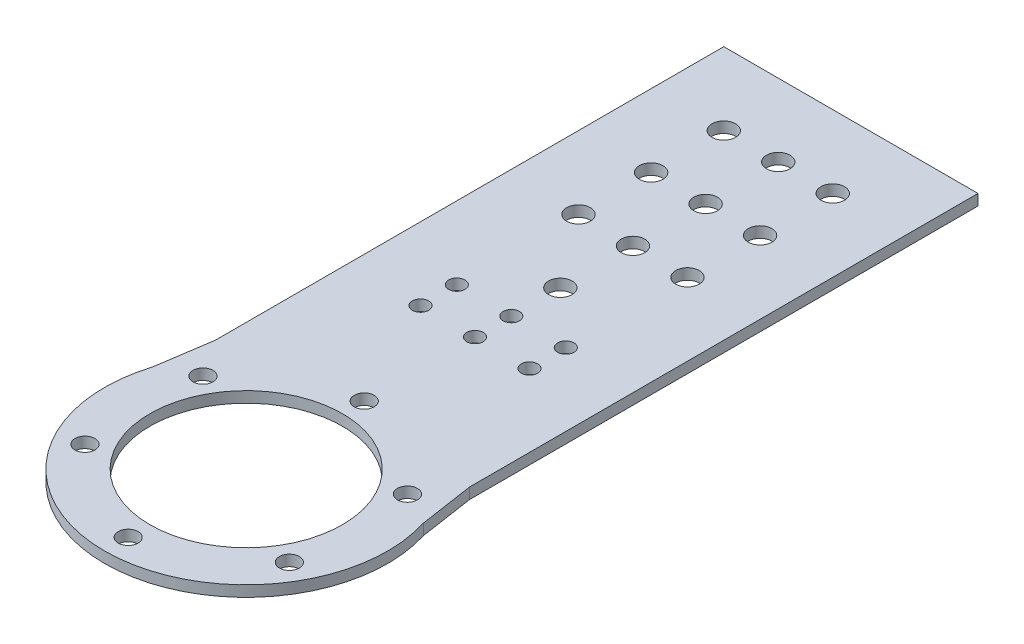
SolidWorks part; units mm, degrees
ref_plane "Front Plane" through (0, 0, 0) normal (0, 0, 1) x (1, 0, 0)
ref_plane "Top Plane" through (0, 0, 0) normal (0, 1, 0) x (1, 0, 0)
ref_plane "Right Plane" through (0, 0, 0) normal (1, 0, 0) x (0, 0, -1)
sketch "Sketch1" plane through (0, 0, 0) normal (0, 1, 0) x (1, 0, 0)
  circle A0 centre (0, 0) radius 45 construction
  circle A1 centre (0, 0) radius 39
  circle A2 centre (0, 0) radius 26.5
  circle A3 centre (0, 0) radius 32.5 construction
  dimension "D1" = 90
  dimension "D2" = 65
  dimension "D3" = 78
  dimension "D4" = 53
extrude "Boss-Extrude1" add sketch "Sketch1" along normal mid plane 3
sketch "Sketch3" plane through (0, 0, 0) normal (0, 1, 0) x (1, 0, 0)
  line L0 (0, 0) -> (0, 78) construction
  line L2 (-25, 78) -> (25, 78)
  line L3 (-25, 78) -> (-25, 26.5)
  line L4 (-25, 26.5) -> (25, 26.5)
  line L5 (25, 78) -> (25, 26.5)
  line L6 (0, 26.5) -> (0, 78) construction
  line L7 (-25, 52.25) -> (25, 52.25) construction
  circle A0 centre (0, 0) radius 26.5 construction
  point P3 (0, 52.25)
  dimension "D1" = 78
  dimension "D2" = 50
extrude "Boss-Extrude2" add sketch "Sketch3" along normal mid plane 3
sketch "Sketch4" plane through (0, 0, 0) normal (0, 1, 0) x (1, 0, 0)
  line L0 (-25, 53.9666) -> (-37.4668, 10.8276)
  line L1 (-25, 78) -> (-25, 29.9333) construction
  line L2 (-37.4668, 10.8276) -> (-25, 29.9333)
  line L3 (-25, 29.9333) -> (-25, 53.9666)
  line L4 (0, 0) -> (0, 78) construction
  line L5 (25, 78) -> (-25, 78) construction
  line L6 (37.4668, 10.8276) -> (25, 29.9333)
  line L7 (25, 53.9666) -> (37.4668, 10.8276)
  line L8 (25, 29.9333) -> (25, 53.9666)
  circle A0 centre (0, 0) radius 39 construction
extrude "Boss-Extrude3" [suppressed] add sketch "Sketch4" along normal mid plane 3
sketch "Sketch6" plane through (0, 0, 0) normal (0, 1, 0) x (1, 0, 0)
  line L0 (0, 0) -> (0, 96.5) construction
  line L1 (-35, 166.5) -> (-35, 26.5)
  line L2 (-35, 166.5) -> (35, 166.5)
  line L4 (35, 166.5) -> (35, 26.5)
  line L5 (0, 26.5) -> (0, 166.5) construction
  line L6 (-35, 96.5) -> (35, 96.5) construction
  line L7 (-35, 26.5) -> (-39, 0)
  line L8 (35, 26.5) -> (39, 0)
  line L9 (39, 0) -> (16.5208, 26.5)
  line L10 (16.5208, 26.5) -> (-14.9815, 26.5)
  line L11 (-14.9815, 26.5) -> (-39, 0)
  circle A0 centre (0, 0) radius 26.5 construction
  circle A1 centre (0, 0) radius 39 construction
  dimension "D1" = 70
  dimension "D2" = 140
extrude "Boss-Extrude4" add sketch "Sketch6" along normal mid plane 3
sketch "Sketch2" plane through (0, 0, 0) normal (0, 1, 0) x (1, 0, 0)
  circle A0 centre (0, 0) radius 32.5 construction
  circle A1 centre (0, 32.5) radius 2.75
  dimension "D1" = 65
  dimension "D2" = 5.5
extrude "Cut-Extrude1" cut sketch "Sketch2" against normal through all both and the other way through all contours A1
pattern_circular "CirPattern1" count 6 over 360 about axis through (0, 0, 0) along (0, 1, 0) of "Cut-Extrude1"
sketch "Sketch5" plane through (0, 1.5, 0) normal (0, 1, 0) x (1, 0, 0)
  line L0 (-25, 73) -> (25, 73) construction
  line L4 (35, 166.5) -> (-35, 166.5) construction
  circle A0 centre (0, 73) radius 2.25
  dimension "D1" = 4.5
  dimension "D3" = 93.5
extrude "Cut-Extrude2" cut sketch "Sketch5" against normal through all both and the other way through all
pattern_linear "LPattern1" count 2 spacing 15 along (1, 0, 0) count 2 spacing 10 along (0, 0, 1) of "Cut-Extrude2"
pattern_linear "LPattern2" count 2 spacing 15 along (-1, 0, 0) count 2 spacing 10 along (0, 0, 1) of "Cut-Extrude2"
sketch "Sketch7" plane through (0, 1.5, 0) normal (0, 1, 0) x (1, 0, 0)
  line L0 (0, 0) -> (0, 166.5) construction
  line L1 (35, 166.5) -> (-35, 166.5) construction
  line L2 (-15, 146.5) -> (15, 146.5) construction
  circle A0 centre (-15, 146.5) radius 3.25
  circle A1 centre (15, 146.5) radius 3.25
  point P8 (0, 146.5)
  dimension "D1" = 6.5
  dimension "D2" = 20
  dimension "D3" = 30
extrude "Cut-Extrude3" cut sketch "Sketch7" against normal through all both and the other way through all
pattern_linear "LPattern3" count 3 spacing 20 along (0, 0, 1) of "Cut-Extrude3"
sketch "Sketch8" plane through (0, 1.5, 0) normal (0, 1, 0) x (1, 0, 0)
  line L0 (0, 0) -> (0, 166.5) construction
  line L1 (35, 166.5) -> (-35, 166.5) construction
  circle A0 centre (0, 146.5) radius 3.25
  dimension "D1" = 6.5
  dimension "D2" = 20
extrude "Cut-Extrude4" cut sketch "Sketch8" against normal blind 10
pattern_linear "LPattern4" count 4 spacing 20 along (0, 0, 1) of "Cut-Extrude4"
